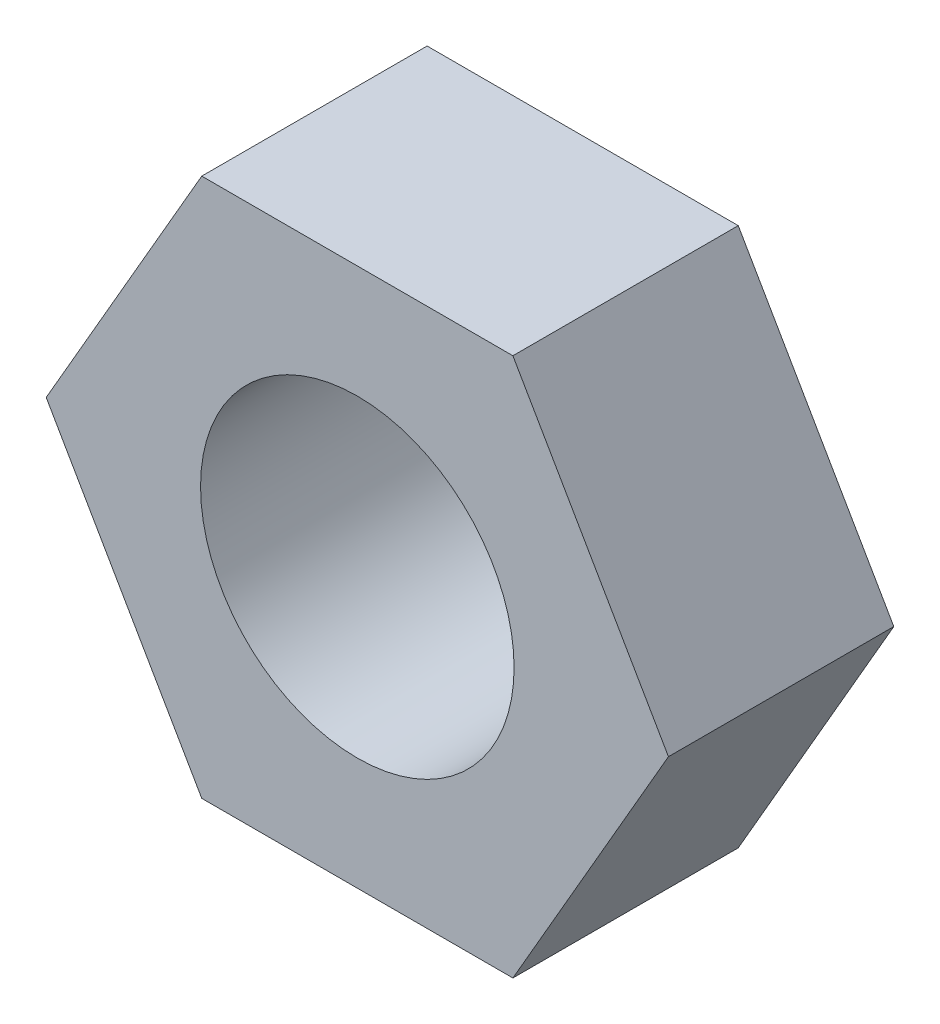
SolidWorks part; units mm, degrees
ref_plane "Front Plane" through (0, 0, 0) normal (0, 0, 1) x (1, 0, 0)
ref_plane "Top Plane" through (0, 0, 0) normal (0, 1, 0) x (1, 0, 0)
ref_plane "Right Plane" through (0, 0, 0) normal (1, 0, 0) x (0, 0, -1)
sketch "Sketch1" plane through (0, 0, 0) normal (0, 0, 1) x (1, 0, 0)
  line L1 (6.3012, 0) -> (3.1506, 5.457)
  line L2 (3.1506, 5.457) -> (-3.1506, 5.457)
  line L3 (-3.1506, 5.457) -> (-6.3012, 0)
  line L4 (-6.3012, 0) -> (-3.1506, -5.457)
  line L5 (-3.1506, -5.457) -> (3.1506, -5.457)
  line L6 (3.1506, -5.457) -> (6.3012, 0)
  circle A0 centre (0, 0) radius 5.457 construction
  dimension "D1" = 10.914
extrude "Boss-Extrude1" add sketch "Sketch1" along normal blind 4.564
sketch "Sketch2" plane through (0, 0, 4.564) normal (0, 0, 1) x (1, 0, 0)
  circle A0 centre (0, 0) radius 3.175
  dimension "D1" = 6.35
extrude "Cut-Extrude1" cut sketch "Sketch2" against normal blind 4.564
